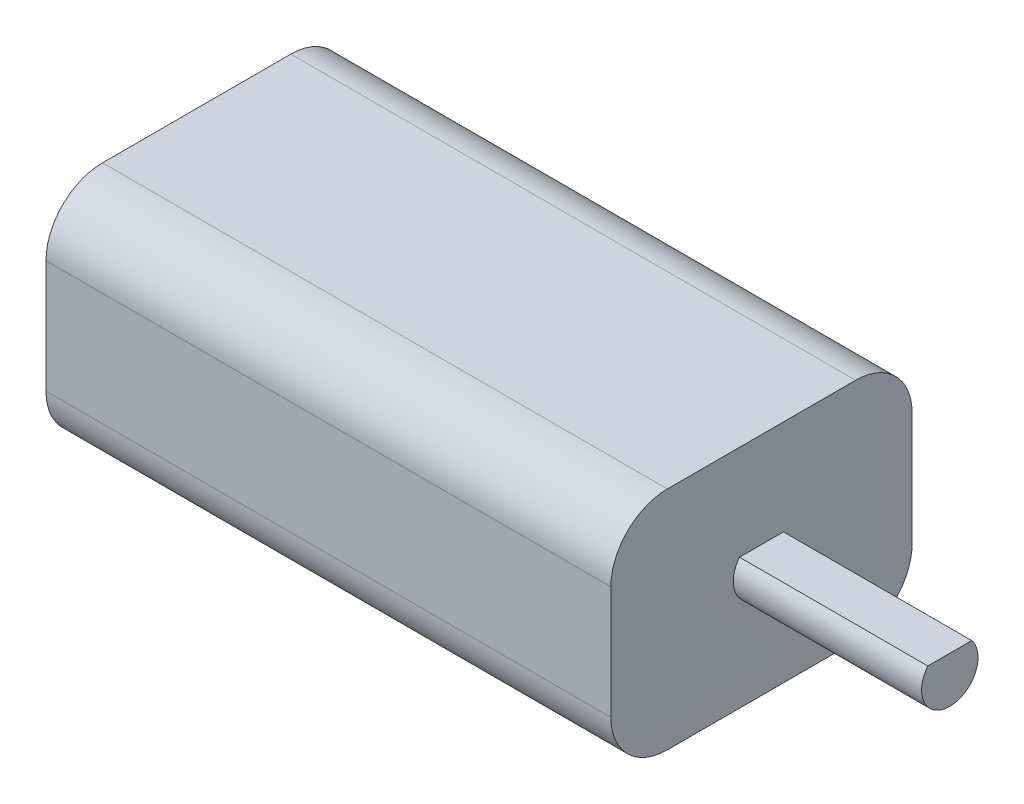
SolidWorks part; units mm, degrees
ref_plane "Front Plane" through (0, 0, 0) normal (0, 0, 1) x (1, 0, 0)
ref_plane "Top Plane" through (0, 0, 0) normal (0, 1, 0) x (1, 0, 0)
ref_plane "Right Plane" through (0, 0, 0) normal (1, 0, 0) x (0, 0, -1)
sketch "Sketch1" plane through (0, 0, 0) normal (0, 1, 0) x (1, 0, 0)
  line L1 (-15, -8) -> (15, -8)
  line L2 (-15, -8) -> (-15, 8)
  line L3 (-15, 8) -> (15, 8)
  line L4 (15, -8) -> (15, 8)
  line L5 (-15, -8) -> (15, 8) construction
  line L6 (-15, 8) -> (15, -8) construction
  point P0 (0, 0)
  dimension "D1" = 30
  dimension "D2" = 16
extrude "Boss-Extrude1" add sketch "Sketch1" along normal blind 12
fillet "Fillet2" radius 3 4 edges at (0, 0, 8) (0, 12, 8) (0, 12, -8) (0, 0, -8)
sketch "Sketch3" plane through (15, 0, 0) normal (1, 0, 0) x (0, 0, -1)
  line L0 (-5, 12) -> (5, 12) construction
  line L1 (8, 9) -> (8, 3) construction
  line L2 (-1.1666, 6.9429) -> (1.1666, 6.9429)
  arc A0 (-1.1666, 6.9429) -> (1.1666, 6.9429) centre (0, 6) ccw
  point P2 (0, 12)
  point P5 (8, 6)
  dimension "D1" = 6
  dimension "D2" = 8
extrude "Boss-Extrude3" add sketch "Sketch3" along normal blind 10
